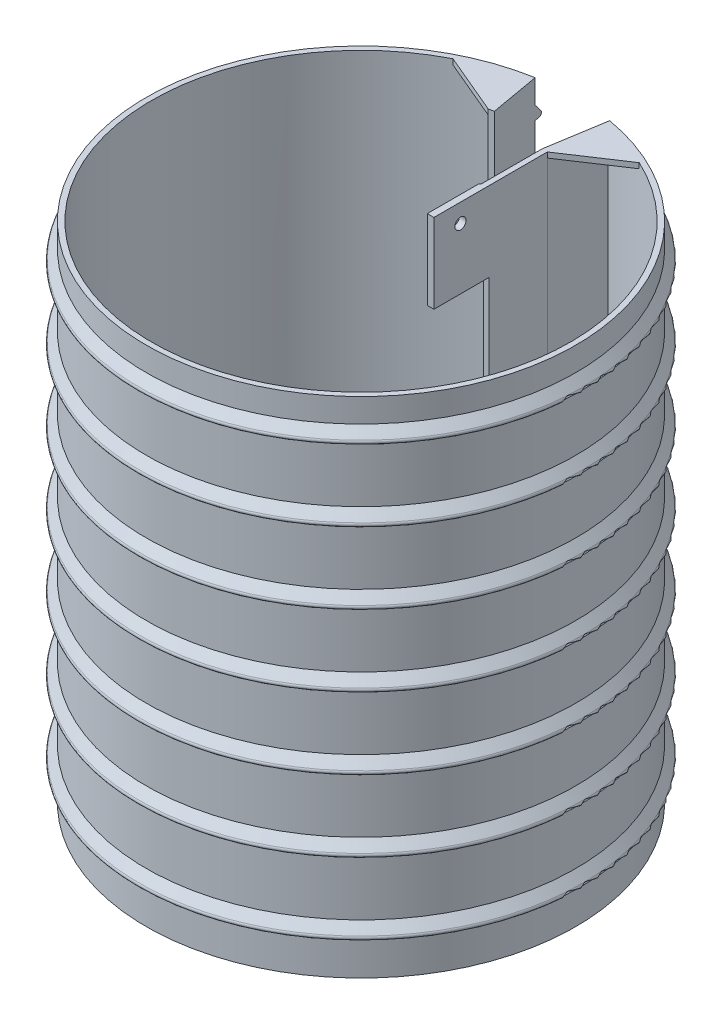
SolidWorks part; units mm, degrees
ref_plane "Plano frontal" through (0, 0, 0) normal (0, 0, 1) x (1, 0, 0)
ref_plane "Plano superior" through (0, 0, 0) normal (0, 1, 0) x (1, 0, 0)
ref_plane "Plano direito" through (0, 0, 0) normal (1, 0, 0) x (0, 0, -1)
sketch "Esboço1" plane through (0, 0, 0) normal (0, 1, 0) x (1, 0, 0)
  line L0 (0, 97.5906) -> (0, -93.5714) construction
  line L1 (-13.7182, 77.7998) -> (-14.0655, 79.7694)
  line L2 (13.7182, 77.7998) -> (14.0655, 79.7694)
  line L4 (12.5, 35.8) -> (12.5, 57.8)
  line L5 (10.5, 35.8) -> (10.5, 57.8)
  line L6 (10.5, 57.8) -> (13.7182, 77.7998)
  line L7 (12.5, 57.8) -> (15.6591, 77.4325)
  line L8 (12.5, 35.8) -> (10.5, 35.8)
  arc A0 (-14.0655, 79.7694) -> (14.0655, 79.7694) centre (0, 0) ccw
  arc A1 (-13.7182, 77.7998) -> (15.6591, 77.4325) centre (0, 0) ccw
  dimension "D1" = 10
  dimension "D3" = 81
  dimension "D4" = 79
  dimension "D2" = 10
  dimension "D5" = 2
  dimension "D6" = 1.9746
  dimension "D7" = 22
  dimension "D8" = 19.6325
extrude "Ressalto-extrusão1" add sketch "Esboço1" along normal blind 190
sketch "Esboço2" plane through (0, 0, 0) normal (0.9848, 0, -0.1736) x (-0.1736, 0, -0.9848)
  line L1 (81, 190) -> (81, 0) construction
  line L2 (81, 14) -> (82.9194, 14)
  line L4 (79, 0) -> (81, 0) construction
  line L5 (81, 19) -> (81, 14)
  line L6 (83.7002, 15.6247) -> (81, 19)
  arc A0 (82.9194, 14) -> (83.7002, 15.6247) centre (82.9194, 15) ccw
  point P10 (85, 14)
  point P13 (85, 14)
  dimension "D4" = 1
  dimension "D1" = 4
  dimension "D2" = 14
  dimension "D3" = 5
ref_plane "Plano1" through (0, 13, 0) normal (0, 1, 0) x (1, 0, 0)
sketch "Esboço3" plane through (0, 13, 0) normal (0, 1, 0) x (1, 0, 0)
  arc A0 (-14.1523, 80.2618) -> (14.1523, 80.2618) centre (0, 0) ccw
  dimension "D1" = 163
sweep "Varredura1" add profiles "Esboço2" path "Esboço3"
pattern_linear "Padrão linear1" count 7 spacing 27 along (0, 1, 0) of "Varredura1"
sketch "Esboço4" plane through (0, 190, 0) normal (0, 1, 0) x (1, 0, 0)
  line L2 (10.5, 35.8) -> (10.5, 35)
  line L3 (10.5, 35) -> (10, 34.5)
  line L5 (10, 34.5) -> (10, 15)
  line L8 (12.5, 15) -> (12.5, 35.8)
  line L9 (10.5, 35.8) -> (12.5, 35.8)
  line L10 (10, 15) -> (12.5, 15)
extrude "Ressalto-extrusão2" add sketch "Esboço4" against normal blind 30
sketch "Esboço5" plane through (12.5, 0, 0) normal (1, 0, 0) x (0, 0, -1)
  line L2 (15, 190) -> (57.8, 190) construction
  line L6 (15, 160) -> (15, 190) construction
  circle A0 centre (25, 183) radius 2.1
  dimension "D1" = 4.2
  dimension "D2" = 10
  dimension "D3" = 7
extrude "Corte-extrusão1" cut sketch "Esboço5" against normal up to next contours A0
ref_plane "Plano2" through (-13.7182, 0, -77.7998) normal (0, -1, 0) x (-1, 0, 0)
sketch "Esboço6" plane through (0, 190, 0) normal (0, 1, 0) x (1, 0, 0)
  line L0 (-13.7182, 77.7998) -> (-10.7662, 61.0581)
  line L1 (-10.7662, 61.0581) -> (-12.7358, 60.7108)
  line L2 (-12.7358, 60.7108) -> (-16.2194, 77.3171)
  arc A0 (-13.7182, 77.7998) -> (15.6591, 77.4325) centre (0, 0) ccw construction
  arc A1 (-13.7182, 77.7998) -> (-16.2194, 77.3171) centre (0, 0) ccw
  dimension "D2" = 2
  dimension "D1" = 17
extrude "Ressalto-extrusão3" add sketch "Esboço6" against normal blind 165
sketch "Esboço7" plane through (0, 190, 0) normal (0, 1, 0) x (1, 0, 0)
  line L0 (-12.7358, 60.7108) -> (-35.7647, 70.4407)
  line L1 (12.5, 57.8) -> (33.3295, 71.625)
  line L11 (-16.2194, 77.3171) -> (-12.7358, 60.7108)
  line L12 (-12.7358, 60.7108) -> (-10.7662, 61.0581)
  line L13 (-10.7662, 61.0581) -> (-14.0655, 79.7694)
  line L14 (14.0655, 79.7694) -> (13.7182, 77.7998)
  line L15 (13.7182, 77.7998) -> (10.5, 57.8)
  line L16 (10.5, 57.8) -> (10.5, 35)
  line L17 (10.5, 35) -> (10, 34.5)
  line L18 (10, 34.5) -> (10, 15)
  line L19 (10, 15) -> (12.5, 15)
  line L20 (12.5, 15) -> (12.5, 57.8)
  line L21 (12.5, 57.8) -> (15.6591, 77.4325)
  line L22 (-16.2194, 77.3171) -> (-12.7358, 60.7108)
  line L25 (14.0655, 79.7694) -> (13.7182, 77.7998)
  line L28 (10.5, 35) -> (10, 34.5)
  line L32 (12.5, 57.8) -> (15.6591, 77.4325)
  arc A0 (33.3295, 71.625) -> (15.6591, 77.4325) centre (0, 0) ccw
  arc A2 (-16.2194, 77.3171) -> (15.6591, 77.4325) centre (0, 0) ccw
  arc A3 (-14.0655, 79.7694) -> (14.0655, 79.7694) centre (0, 0) ccw
  arc A4 (-16.2194, 77.3171) -> (-35.7647, 70.4407) centre (0, 0) ccw
  arc M16 (15.6591, 77.4325) -> (-16.2194, 77.3171) centre (0, 0) cw
  line M17 (-16.2194, 77.3171) -> (-12.7358, 60.7108)
  line M28 (12.5, 57.8) -> (15.6591, 77.4325)
  dimension "D2" = 25
  dimension "D3" = 25
  dimension "D1" = 0
extrude "Ressalto-extrusão4" add sketch "Esboço7" against normal blind 2 contours L1 M28 M16 | L0 M17 M16
